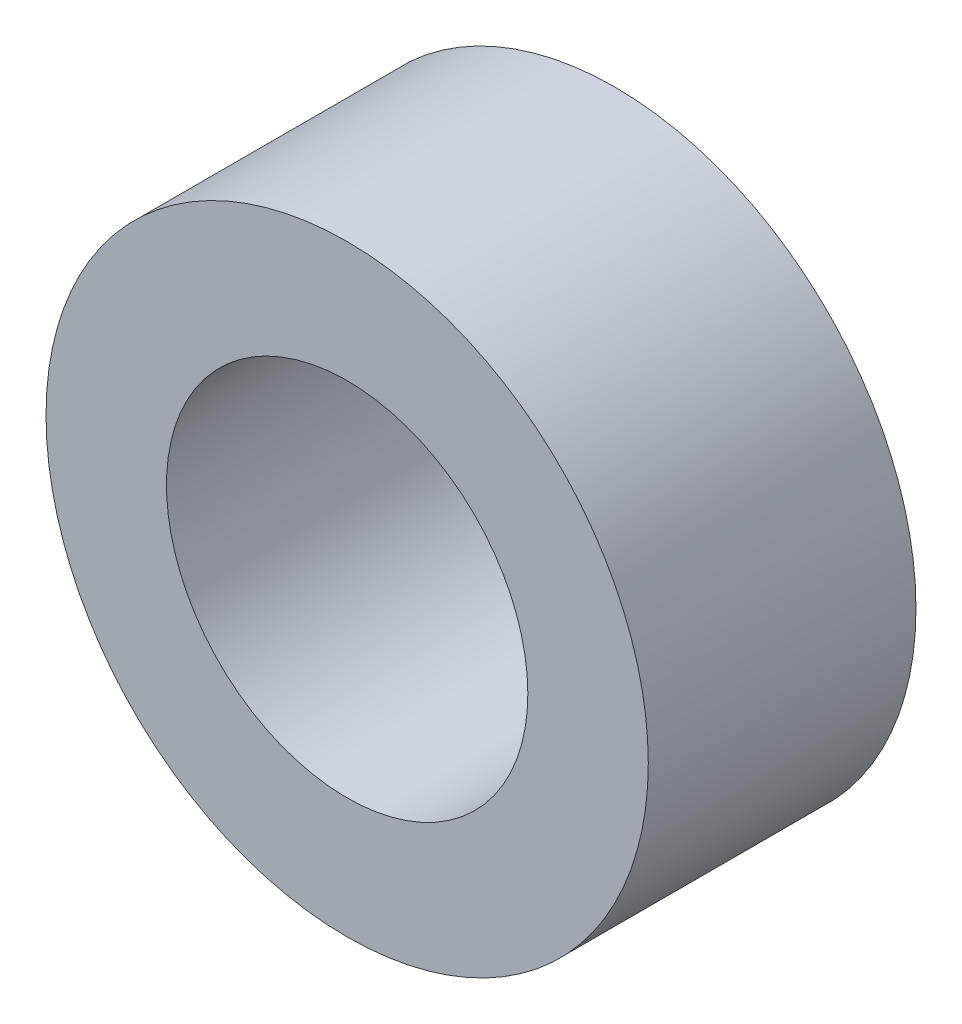
SolidWorks part; units mm, degrees
ref_plane "Front Plane" through (0, 0, 0) normal (0, 0, 1) x (1, 0, 0)
ref_plane "Top Plane" through (0, 0, 0) normal (0, 1, 0) x (1, 0, 0)
ref_plane "Right Plane" through (0, 0, 0) normal (1, 0, 0) x (0, 0, -1)
sketch "Sketch1" plane through (0, 0, 0) normal (0, 0, 1) x (1, 0, 0)
  circle A0 centre (0, 0) radius 2.25
  circle A1 centre (0, 0) radius 1.35
  dimension "OD" = 4.5
  dimension "ID" = 2.7
extrude "Extrude1" add sketch "Sketch1" along normal mid plane 2
sketch "Sketch2" plane through (0, 0, 0) normal (1, 0, 0) x (0, 0, -1)
  line L0 (-1, -1.35) -> (1, -1.35) construction
  line L3 (1, 1.35) -> (-1, 1.35) construction
  line L5 (-1, -1.35) -> (1, -1.35)
  line L6 (1, 1.35) -> (-1, 1.35)
sketch "Sketch4" plane through (0, 0, 1) normal (0, 0, 1) x (1, 0, 0)
  line L0 (0, 0) -> (-0.9546, 0.9546)
  line L1 (0, -7.15) -> (0, 7.15) construction
  circle A0 centre (0, 0) radius 1.35 construction
  dimension "D1" = 45
